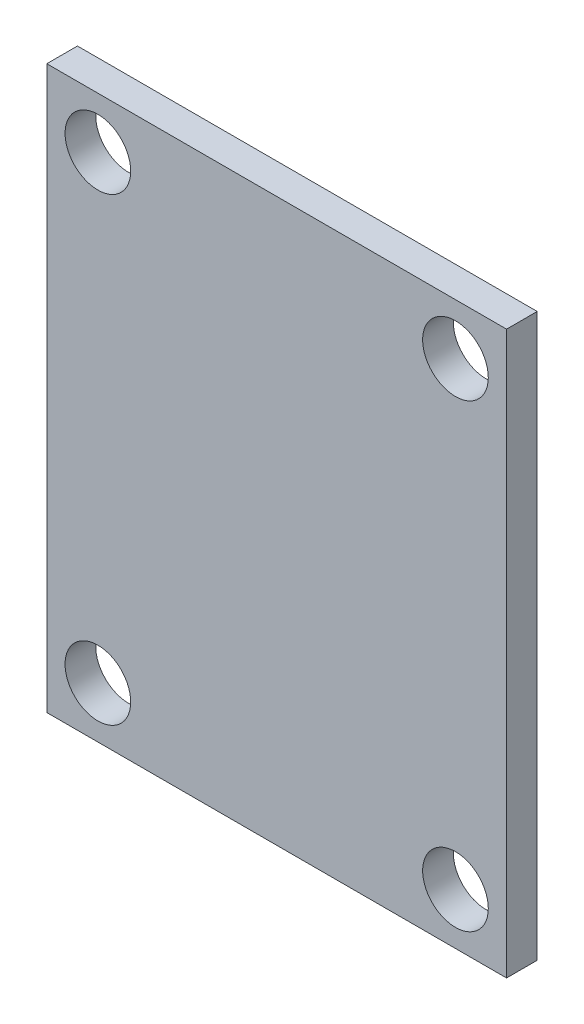
SolidWorks part; units mm, degrees
ref_plane "Front Plane" through (0, 0, 0) normal (0, 0, 1) x (1, 0, 0)
ref_plane "Top Plane" through (0, 0, 0) normal (0, 1, 0) x (1, 0, 0)
ref_plane "Right Plane" through (0, 0, 0) normal (1, 0, 0) x (0, 0, -1)
sketch "Sketch1" plane through (0, 0, 0) normal (0, 0, 1) x (1, 0, 0)
  line L1 (-11.43, 13.97) -> (11.43, 13.97)
  line L2 (-11.43, 13.97) -> (-11.43, -13.97)
  line L3 (-11.43, -13.97) -> (11.43, -13.97)
  line L4 (11.43, 13.97) -> (11.43, -13.97)
  line L5 (-11.43, 13.97) -> (11.43, -13.97) construction
  line L6 (-11.43, -13.97) -> (11.43, 13.97) construction
  line L7 (-8.89, 11.43) -> (8.89, 11.43) construction
  line L8 (-8.89, 11.43) -> (-8.89, -11.43) construction
  line L9 (-8.89, -11.43) -> (8.89, -11.43) construction
  line L10 (8.89, 11.43) -> (8.89, -11.43) construction
  line L11 (-8.89, 11.43) -> (8.89, -11.43) construction
  line L12 (-8.89, -11.43) -> (8.89, 11.43) construction
  circle A0 centre (-8.89, 11.43) radius 1.632
  circle A1 centre (8.89, 11.43) radius 1.632
  circle A2 centre (8.89, -11.43) radius 1.632
  circle A3 centre (-8.89, -11.43) radius 1.632
  point P0 (0, 0)
  point P6 (0, 0)
  dimension "D5" = 3.2639
  dimension "D1" = 27.94
  dimension "D2" = 22.86
  dimension "D3" = 17.78
  dimension "D4" = 22.86
extrude "Boss-Extrude1" add sketch "Sketch1" along normal blind 1.524
